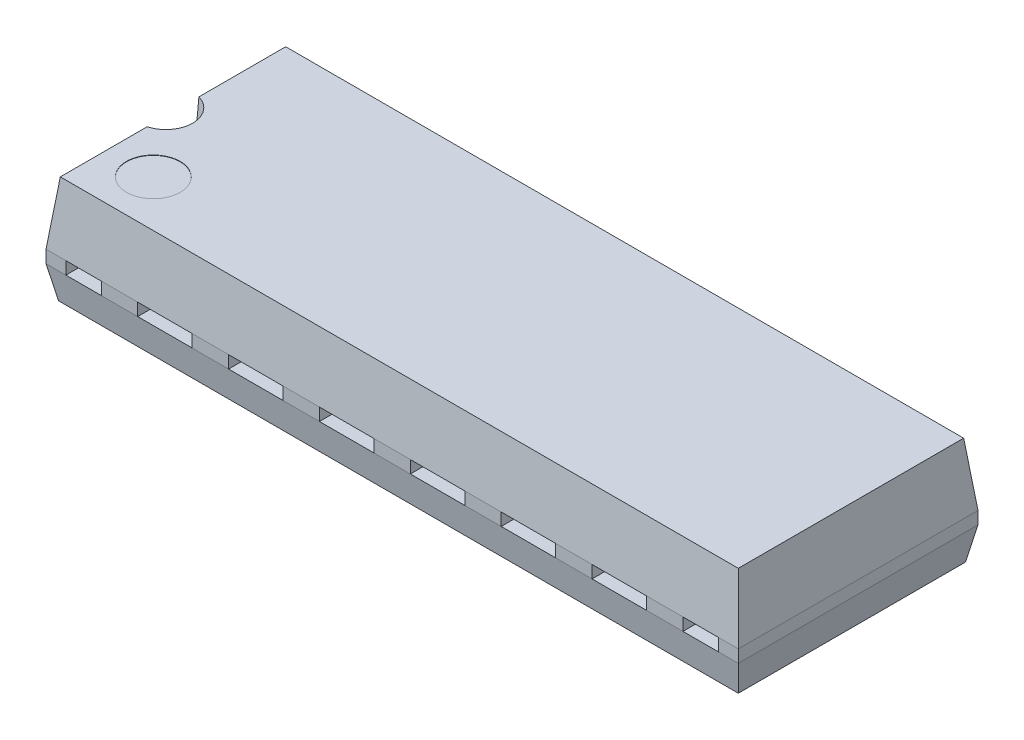
SolidWorks part; units mm, degrees
ref_plane "Front Plane" through (0, 0, 0) normal (0, 0, 1) x (1, 0, 0)
ref_plane "Top Plane" through (0, 0, 0) normal (0, 1, 0) x (1, 0, 0)
ref_plane "Right Plane" through (0, 0, 0) normal (1, 0, 0) x (0, 0, -1)
sketch "Sketch1" plane through (0, 0, 0) normal (0, 1, 0) x (1, 0, 0)
  line L1 (-9.675, 3.35) -> (9.675, 3.35)
  line L2 (-9.675, 3.35) -> (-9.675, -3.35)
  line L3 (-9.675, -3.35) -> (9.675, -3.35)
  line L4 (9.675, 3.35) -> (9.675, -3.35)
  line L5 (-9.675, 3.35) -> (9.675, -3.35) construction
  line L6 (-9.675, -3.35) -> (9.675, 3.35) construction
  point P0 (0, 0)
  dimension "D1" = 19.35
  dimension "D2" = 6.7
ref_plane "Plane1" through (0, 1.75, 0) normal (0, 1, 0) x (-1, 0, 0)
sketch "Sketch2" plane through (0, 1.75, 0) normal (0, 1, 0) x (-1, 0, 0)
  line L1 (-9.475, 3.15) -> (9.475, 3.15)
  line L2 (-9.475, 3.15) -> (-9.475, -3.15)
  line L3 (-9.475, -3.15) -> (9.475, -3.15)
  line L4 (9.475, 3.15) -> (9.475, -3.15)
  line L5 (-9.475, 3.15) -> (9.475, -3.15) construction
  line L6 (-9.475, -3.15) -> (9.475, 3.15) construction
  line L7 (-9.675, -3.35) -> (-9.675, 3.35) construction
  line L8 (9.675, 3.35) -> (-9.675, 3.35) construction
  point P0 (0, 0)
  dimension "D1" = 0.2
  dimension "D2" = 0.2
loft "Loft1" add profiles "Sketch2", "Sketch1"
sketch "Sketch3" plane through (0, 0, 0) normal (0, -1, 0) x (1, 0, 0)
  line L4 (9.675, -3.35) -> (9.675, 3.35)
  line L5 (9.675, 3.35) -> (-9.675, 3.35)
  line L6 (-9.675, 3.35) -> (-9.675, -3.35)
  line L7 (-9.675, -3.35) -> (9.675, -3.35)
  line L8 (9.675, -3.35) -> (9.675, 3.35)
  line L9 (9.675, 3.35) -> (-9.675, 3.35)
  line L10 (-9.675, 3.35) -> (-9.675, -3.35)
  line L11 (-9.675, -3.35) -> (9.675, -3.35)
  dimension "D1" = 0
extrude "Extrude1" add sketch "Sketch3" along normal blind 0.35
sketch "Sketch4" plane through (0, -0.35, 0) normal (0, -1, 0) x (1, 0, 0)
  line L4 (-9.675, -3.35) -> (9.675, -3.35)
  line L5 (9.675, -3.35) -> (9.675, 3.35)
  line L6 (9.675, 3.35) -> (-9.675, 3.35)
  line L7 (-9.675, 3.35) -> (-9.675, -3.35)
  line L8 (-9.675, -3.35) -> (9.675, -3.35)
  line L9 (9.675, -3.35) -> (9.675, 3.35)
  line L10 (9.675, 3.35) -> (-9.675, 3.35)
  line L11 (-9.675, 3.35) -> (-9.675, -3.35)
  dimension "D1" = 0
ref_plane "Plane2" through (0, -1.25, 0) normal (0, 1, 0) x (-1, 0, 0)
sketch "Sketch5" plane through (0, -1.25, 0) normal (0, 1, 0) x (-1, 0, 0)
  line L0 (9.675, 3.35) -> (9.675, -3.35) construction
  line L1 (9.5, 3.175) -> (-9.5, 3.175)
  line L2 (9.5, 3.175) -> (9.5, -3.175)
  line L3 (9.5, -3.175) -> (-9.5, -3.175)
  line L4 (-9.5, 3.175) -> (-9.5, -3.175)
  line L5 (9.5, 3.175) -> (-9.5, -3.175) construction
  line L6 (9.5, -3.175) -> (-9.5, 3.175) construction
  line L7 (-9.675, 3.35) -> (9.675, 3.35) construction
  point P0 (0, 0)
  dimension "D1" = 0.175
  dimension "D2" = 0.175
loft "Loft2" add profiles "Sketch4", "Sketch5"
sketch "Sketch7" plane through (0, 1.75, 0) normal (0, 1, 0) x (1, 0, 0)
  line L0 (-9.675, 3.35) -> (-9.675, -3.35) construction
  circle A0 centre (-9.675, 0) radius 0.75
  dimension "D1" = 1.5
extrude "Extrude2" cut sketch "Sketch7" against normal blind 0.75
sketch "Sketch8" plane through (0, 1.75, 0) normal (0, 1, 0) x (1, 0, 0)
  line L0 (-9.475, -3.15) -> (9.475, -3.15) construction
  line L1 (-9.475, -0.7228) -> (-9.475, -3.15) construction
  circle A0 centre (-8.175, -1.85) radius 0.75
  dimension "D1" = 1.5
  dimension "D2" = 1.3
  dimension "D3" = 1.3
extrude "Extrude5" cut sketch "Sketch8" against normal blind 0.01
sketch "Sketch11" plane through (0, 0, 3.35) normal (0, 0, 1) x (1, 0, 0)
  line L0 (-4.572, 0) -> (-3.048, 0)
  line L1 (-2.032, 0) -> (-0.508, 0)
  line L2 (-2.032, 0) -> (-2.032, -0.35)
  line L3 (-2.032, -0.35) -> (-0.508, -0.35)
  line L4 (-0.508, 0) -> (-0.508, -0.35)
  line L5 (-2.032, 0) -> (-0.508, -0.35) construction
  line L6 (-2.032, -0.35) -> (-0.508, 0) construction
  line L7 (0.508, 0) -> (2.032, 0)
  line L8 (0.508, 0) -> (0.508, -0.35)
  line L9 (0.508, -0.35) -> (2.032, -0.35)
  line L10 (2.032, 0) -> (2.032, -0.35)
  line L11 (0.508, 0) -> (2.032, -0.35) construction
  line L12 (0.508, -0.35) -> (2.032, 0) construction
  line L13 (9.675, -0.35) -> (-9.675, -0.35) construction
  line L14 (3.048, -0.0002) -> (4.572, -0.0002)
  line L15 (3.048, -0.0002) -> (3.048, -0.3502)
  line L16 (3.048, -0.3502) -> (4.572, -0.3502)
  line L17 (4.572, -0.0002) -> (4.572, -0.3502)
  line L18 (3.048, -0.3502) -> (4.572, -0.0002) construction
  line L19 (-9.675, 0) -> (9.675, 0) construction
  line L20 (3.048, -0.0002) -> (4.572, -0.3502) construction
  line L21 (5.588, -0.0005) -> (7.112, -0.0005)
  line L22 (5.588, -0.0005) -> (5.588, -0.3505)
  line L23 (5.588, -0.3505) -> (7.112, -0.3505)
  line L24 (7.112, -0.0005) -> (7.112, -0.3505)
  line L25 (5.588, -0.3505) -> (7.112, -0.0005) construction
  line L26 (5.588, -0.0005) -> (7.112, -0.3505) construction
  line L27 (8.128, -0.0007) -> (9.652, -0.0007) construction
  line L28 (8.128, -0.0007) -> (8.128, -0.3507)
  line L29 (8.128, -0.3507) -> (9.652, -0.3507) construction
  line L30 (9.652, -0.0007) -> (9.652, -0.3507) construction
  line L31 (8.128, -0.3507) -> (9.652, -0.0007) construction
  line L32 (8.128, -0.0007) -> (9.652, -0.3507) construction
  line L33 (-8.128, 0) -> (-9.1186, 0)
  line L34 (-9.1186, 0) -> (-9.1186, -0.35)
  line L35 (-9.1186, -0.35) -> (-8.128, -0.35)
  line L36 (8.128, -0.0007) -> (9.1186, -0.0007)
  line L37 (9.1186, -0.0007) -> (9.1186, -0.3507)
  line L38 (9.1186, -0.3507) -> (8.128, -0.3507)
  line L69 (-4.572, 0) -> (-4.572, -0.35)
  line L70 (-4.572, -0.35) -> (-3.048, -0.35)
  line L71 (-3.048, 0) -> (-3.048, -0.35)
  line L72 (-4.572, 0) -> (-3.048, -0.35) construction
  line L73 (-4.572, -0.35) -> (-3.048, 0) construction
  line L74 (-7.112, 0) -> (-5.588, 0)
  line L75 (-7.112, 0) -> (-7.112, -0.35)
  line L76 (-7.112, -0.35) -> (-5.588, -0.35)
  line L77 (-5.588, 0) -> (-5.588, -0.35)
  line L78 (-7.112, 0) -> (-5.588, -0.35) construction
  line L79 (-7.112, -0.35) -> (-5.588, 0) construction
  line L80 (-9.652, 0) -> (-8.128, 0) construction
  line L81 (-9.652, 0) -> (-9.652, -0.35) construction
  line L82 (-9.652, -0.35) -> (-8.128, -0.35) construction
  line L83 (-8.128, 0) -> (-8.128, -0.35)
  line L84 (-9.652, 0) -> (-8.128, -0.35) construction
  line L85 (-9.652, -0.35) -> (-8.128, 0) construction
  line L122 (10.668, -0.0009) -> (12.192, -0.0009) [skipped]
  line L123 (10.668, -0.0009) -> (10.668, -0.3509) [skipped]
  line L124 (10.668, -0.3509) -> (12.192, -0.3509) [skipped]
  line L125 (12.192, -0.0009) -> (12.192, -0.3509) [skipped]
  line L126 (13.208, -0.0011) -> (14.732, -0.0011) [skipped]
  line L127 (13.208, -0.0011) -> (13.208, -0.3511) [skipped]
  line L128 (13.208, -0.3511) -> (14.732, -0.3511) [skipped]
  line L129 (14.732, -0.0011) -> (14.732, -0.3511) [skipped]
  line L130 (15.748, -0.0014) -> (17.272, -0.0014) [skipped]
  line L131 (15.748, -0.0014) -> (15.748, -0.3514) [skipped]
  line L132 (15.748, -0.3514) -> (17.272, -0.3514) [skipped]
  line L133 (17.272, -0.0014) -> (17.272, -0.3514) [skipped]
  line L134 (18.288, -0.0016) -> (19.812, -0.0016) [skipped]
  line L135 (18.288, -0.0016) -> (18.288, -0.3516) [skipped]
  line L136 (18.288, -0.3516) -> (19.812, -0.3516) [skipped]
  line L137 (19.812, -0.0016) -> (19.812, -0.3516) [skipped]
  line L138 (20.828, -0.0018) -> (22.352, -0.0018) [skipped]
  line L139 (20.828, -0.0018) -> (20.828, -0.3518) [skipped]
  line L140 (20.828, -0.3518) -> (22.352, -0.3518) [skipped]
  line L141 (22.352, -0.0018) -> (22.352, -0.3518) [skipped]
  line L142 (23.368, -0.0021) -> (24.892, -0.0021) [skipped]
  line L143 (23.368, -0.0021) -> (23.368, -0.3521) [skipped]
  line L144 (23.368, -0.3521) -> (24.892, -0.3521) [skipped]
  line L145 (24.892, -0.0021) -> (24.892, -0.3521) [skipped]
  line L146 (10.668, -0.3509) -> (12.192, -0.0009) construction
  line L147 (10.668, -0.0009) -> (12.192, -0.3509) construction
  line L148 (13.208, -0.3511) -> (14.732, -0.0011) construction
  line L149 (13.208, -0.0011) -> (14.732, -0.3511) construction
  line L150 (15.748, -0.3514) -> (17.272, -0.0014) construction
  line L151 (15.748, -0.0014) -> (17.272, -0.3514) construction
  line L152 (18.288, -0.3516) -> (19.812, -0.0016) construction
  line L153 (18.288, -0.0016) -> (19.812, -0.3516) construction
  line L154 (20.828, -0.3518) -> (22.352, -0.0018) construction
  line L155 (20.828, -0.0018) -> (22.352, -0.3518) construction
  line L156 (23.368, -0.3521) -> (24.892, -0.0021) construction
  line L157 (23.368, -0.0021) -> (24.892, -0.3521) construction
  line L158 (-12.192, 0) -> (-10.668, 0) [skipped]
  line L159 (-12.192, 0) -> (-12.192, -0.35) [skipped]
  line L160 (-12.192, -0.35) -> (-10.668, -0.35) [skipped]
  line L161 (-10.668, 0) -> (-10.668, -0.35) [skipped]
  line L162 (-14.732, 0) -> (-13.208, 0) [skipped]
  line L163 (-14.732, 0) -> (-14.732, -0.35) [skipped]
  line L164 (-14.732, -0.35) -> (-13.208, -0.35) [skipped]
  line L165 (-13.208, 0) -> (-13.208, -0.35) [skipped]
  line L166 (-17.272, 0) -> (-15.748, 0) [skipped]
  line L167 (-17.272, 0) -> (-17.272, -0.35) [skipped]
  line L168 (-17.272, -0.35) -> (-15.748, -0.35) [skipped]
  line L169 (-15.748, 0) -> (-15.748, -0.35) [skipped]
  line L170 (-19.812, 0) -> (-18.288, 0) [skipped]
  line L171 (-19.812, 0) -> (-19.812, -0.35) [skipped]
  line L172 (-19.812, -0.35) -> (-18.288, -0.35) [skipped]
  line L173 (-18.288, 0) -> (-18.288, -0.35) [skipped]
  line L174 (-22.352, 0) -> (-20.828, 0) [skipped]
  line L175 (-22.352, 0) -> (-22.352, -0.35) [skipped]
  line L176 (-22.352, -0.35) -> (-20.828, -0.35) [skipped]
  line L177 (-20.828, 0) -> (-20.828, -0.35) [skipped]
  line L178 (-24.892, 0) -> (-23.368, 0) [skipped]
  line L179 (-24.892, 0) -> (-24.892, -0.35) [skipped]
  line L180 (-24.892, -0.35) -> (-23.368, -0.35) [skipped]
  line L181 (-23.368, 0) -> (-23.368, -0.35) [skipped]
  line L182 (-12.192, 0) -> (-10.668, -0.35) construction
  line L183 (-12.192, -0.35) -> (-10.668, 0) construction
  line L184 (-14.732, 0) -> (-13.208, -0.35) construction
  line L185 (-14.732, -0.35) -> (-13.208, 0) construction
  line L186 (-17.272, 0) -> (-15.748, -0.35) construction
  line L187 (-17.272, -0.35) -> (-15.748, 0) construction
  line L188 (-19.812, 0) -> (-18.288, -0.35) construction
  line L189 (-19.812, -0.35) -> (-18.288, 0) construction
  line L190 (-22.352, 0) -> (-20.828, -0.35) construction
  line L191 (-22.352, -0.35) -> (-20.828, 0) construction
  line L192 (-24.892, 0) -> (-23.368, -0.35) construction
  line L193 (-24.892, -0.35) -> (-23.368, 0) construction
  point P0 (-1.27, -0.175)
  point P5 (1.27, -0.175)
  point P12 (24.13, -0.1771)
  point P13 (3.81, -0.1752)
  point P18 (6.35, -0.1755)
  point P26 (8.89, -0.1757)
  point P31 (-24.13, -0.175)
  point P32 (21.59, -0.1768)
  point P33 (19.05, -0.1766)
  point P34 (16.51, -0.1764)
  point P35 (13.97, -0.1761)
  point P36 (11.43, -0.1759)
  point P37 (-21.59, -0.175)
  point P38 (-19.05, -0.175)
  point P39 (-16.51, -0.175)
  point P40 (-13.97, -0.175)
  point P41 (-11.43, -0.175)
  point P61 (-3.81, -0.175)
  point P66 (-6.35, -0.175)
  point P71 (-8.89, -0.175)
  dimension "D1" = 2.54
  dimension "D2" = 2.54
  dimension "D3" = 1.016
  dimension "D4" = 1.27
  dimension "D5" = 1.016
  dimension "D6" = 1.524
  dimension "D7" = 1.524
  dimension "D8" = 2.54
  dimension "D9" = 0.5334
  dimension "D10" = 0.5334
extrude "Extrude3" cut sketch "Sketch11" against normal blind 1
mirror "Mirror1" about plane through (0, 0, 0) normal (0, 0, 1) of "Extrude3"
